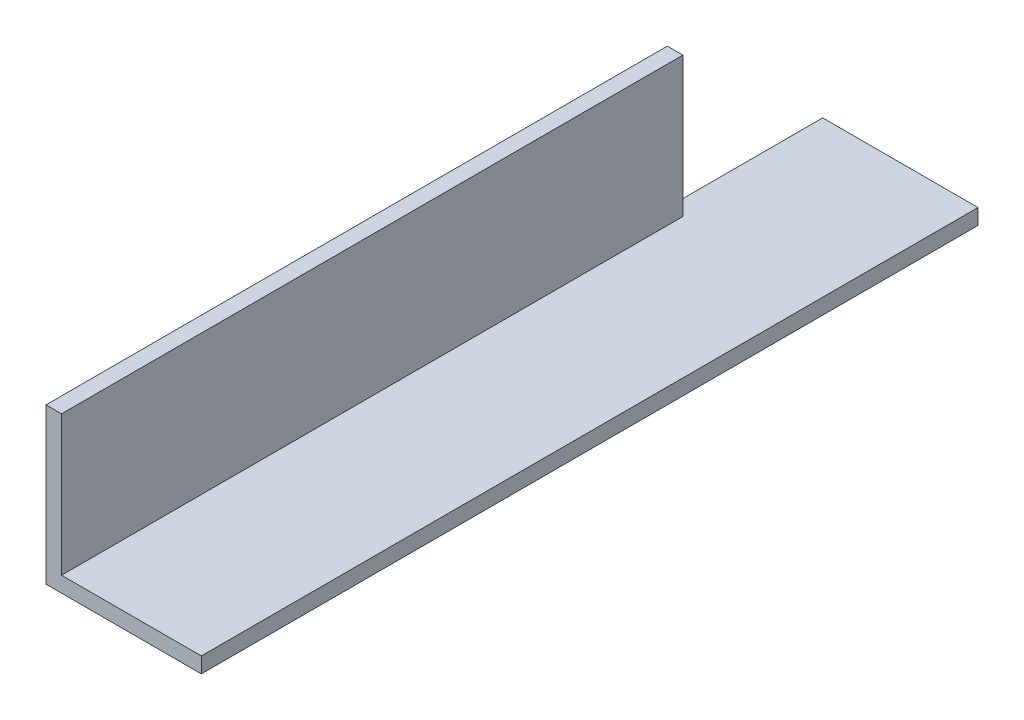
SolidWorks part; units mm, degrees
ref_plane "Front Plane" through (0, 0, 0) normal (0, 0, 1) x (1, 0, 0)
ref_plane "Top Plane" through (0, 0, 0) normal (0, 1, 0) x (1, 0, 0)
ref_plane "Right Plane" through (0, 0, 0) normal (1, 0, 0) x (0, 0, -1)
sketch "Sketch1" plane through (0, 0, 0) normal (0, 0, 1) x (1, 0, 0)
  line L0 (0, 0) -> (0, 20)
  line L1 (0, 0) -> (20, 0)
  line L2 (2, 2) -> (20, 2)
  line L3 (2, 2) -> (2, 20)
  line L4 (0, 20) -> (2, 20)
  line L5 (20, 0) -> (20, 2)
  dimension "D1" = 20
  dimension "D2" = 20
  dimension "D3" = 2
extrude "Boss-Extrude1" add sketch "Sketch1" along normal blind 100
sketch "Sketch2" plane through (2, 0, 0) normal (1, 0, 0) x (0, 0, -1)
  line L0 (0, 2) -> (-20, 2)
  line L1 (-100, 2) -> (0, 2) construction
  line L2 (-20, 2) -> (-20, 20)
  line L3 (-100, 20) -> (0, 20) construction
  line L4 (-20, 20) -> (0, 20)
  line L5 (0, 20) -> (0, 2)
  dimension "D1" = 20
extrude "Cut-Extrude1" cut sketch "Sketch2" against normal through all
